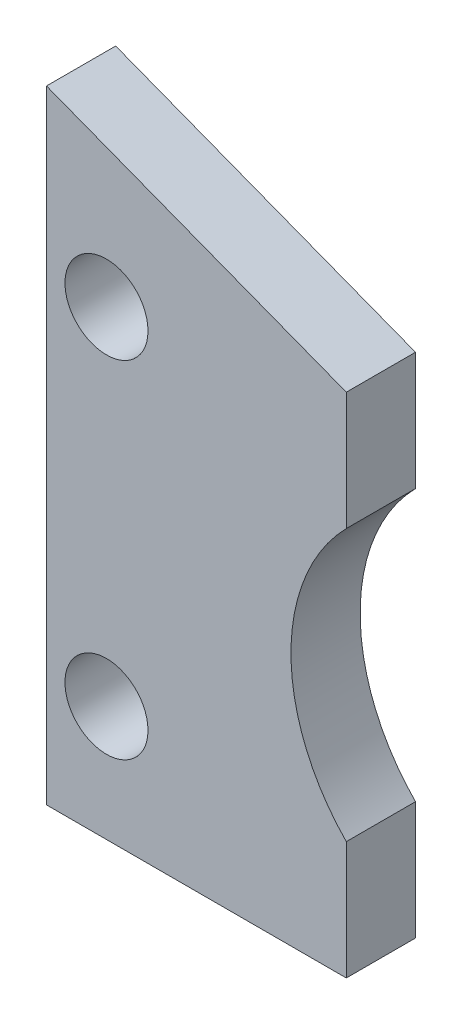
SolidWorks part; units mm, degrees
ref_plane "Front Plane" through (0, 0, 0) normal (0, 0, 1) x (1, 0, 0)
ref_plane "Top Plane" through (0, 0, 0) normal (0, 1, 0) x (1, 0, 0)
ref_plane "Right Plane" through (0, 0, 0) normal (1, 0, 0) x (0, 0, -1)
sketch "Çizim1" plane through (0, 0, 0) normal (0, 0, 1) x (1, 0, 0)
  line L0 (0, 0) -> (0, 135)
  line L1 (0, 135) -> (65, 110)
  line L2 (65, 110) -> (65, 84.3939)
  line L3 (0, 0) -> (65, 0)
  line L4 (65, 0) -> (65, 25.6061)
  arc A0 (65, 25.6061) -> (65, 84.3939) centre (95, 55) cw
  dimension "D1" = 42
  dimension "D2" = 135
  dimension "D3" = 110
  dimension "D4" = 65
  dimension "D5" = 55
  dimension "D6" = 95
  dimension "D7" = 65
extrude "Yükseklik-Ekstrüzyon1" add sketch "Çizim1" along normal mid plane 15
sketch "Çizim2" plane through (0, 0, 7.5) normal (0, 0, 1) x (1, 0, 0)
  circle A0 centre (13, 100) radius 9
  circle A1 centre (13, 25) radius 9
  dimension "D1" = 18
extrude "Kes-Ekstrüzyon1" cut sketch "Çizim2" against normal through all
